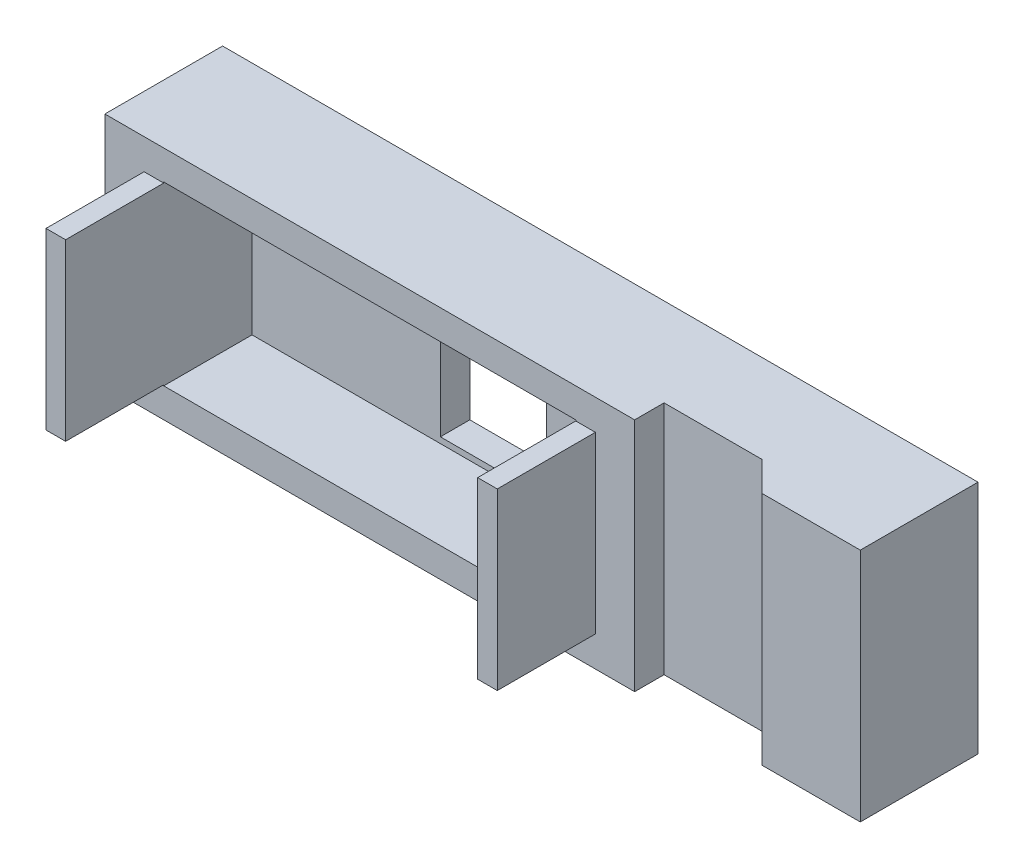
SolidWorks part; units mm, degrees
ref_plane "前视基准面" through (0, 0, 0) normal (0, 0, 1) x (1, 0, 0)
ref_plane "上视基准面" through (0, 0, 0) normal (0, 1, 0) x (1, 0, 0)
ref_plane "右视基准面" through (0, 0, 0) normal (1, 0, 0) x (0, 0, -1)
sketch "草图1" plane through (0, 0, 0) normal (0, 0, 1) x (1, 0, 0)
  line L1 (-13.5, 6) -> (13.5, 6)
  line L2 (-13.5, 6) -> (-13.5, -6)
  line L3 (-13.5, -6) -> (13.5, -6)
  line L4 (13.5, 6) -> (13.5, -6)
  line L5 (-13.5, 6) -> (13.5, -6) construction
  line L6 (-13.5, -6) -> (13.5, 6) construction
  line L7 (-10.5, 4.5) -> (10.5, 4.5)
  line L8 (-10.5, 4.5) -> (-10.5, -4.5)
  line L9 (-10.5, -4.5) -> (10.5, -4.5)
  line L10 (10.5, 4.5) -> (10.5, -4.5)
  line L11 (-10.5, 4.5) -> (10.5, -4.5) construction
  line L12 (-10.5, -4.5) -> (10.5, 4.5) construction
  point P0 (0, 0)
  point P6 (0, 0)
  dimension "D1" = 3
  dimension "D2" = 1.5
  dimension "D3" = 21
  dimension "D4" = 9
extrude "凸台-拉伸1" add sketch "草图1" along normal blind 6
sketch "草图2" plane through (0, 0, 0) normal (0, 0, -1) x (-1, 0, 0)
  line L1 (-10.5, 4.5) -> (10.5, 4.5)
  line L2 (-10.5, 4.5) -> (-10.5, -4.5)
  line L3 (-10.5, -4.5) -> (10.5, -4.5)
  line L4 (10.5, 4.5) -> (10.5, -4.5)
extrude "凸台-拉伸2" add sketch "草图2" against normal blind 1.5
sketch "草图3" plane through (0, 0, 1.5) normal (0, 0, 1) x (1, 0, 0)
  line L0 (10.5, -4.5) -> (10.5, 4.5) construction
  line L1 (-0.9, 4) -> (4.5, 4)
  line L2 (-0.9, 4) -> (-0.9, -4.2)
  line L3 (-0.9, -4.2) -> (4.5, -4.2)
  line L4 (4.5, 4) -> (4.5, -4.2)
  dimension "D1" = 5.4
  dimension "D2" = 8.2
  dimension "D3" = 4
  dimension "D4" = 6
extrude "切除-拉伸1" cut sketch "草图3" against normal through all
sketch "草图4" plane through (0, 0, 6) normal (0, 0, 1) x (1, 0, 0)
  line L0 (-10.5, 4.5) -> (-10.5, -4.5) construction
  line L1 (-10.5, 4.45) -> (-11.5, 4.45)
  line L2 (-10.5, 4.45) -> (-10.5, -4.45)
  line L3 (-10.5, -4.45) -> (-11.5, -4.45)
  line L4 (-11.5, 4.45) -> (-11.5, -4.45)
  line L5 (10.5, -4.5) -> (10.5, 4.5) construction
  line L6 (10.5, 4.45) -> (11.5, 4.45)
  line L7 (10.5, 4.45) -> (10.5, -4.45)
  line L8 (10.5, -4.45) -> (11.5, -4.45)
  line L9 (11.5, 4.45) -> (11.5, -4.45)
  dimension "D1" = 8.9
  dimension "D2" = 8.9
  dimension "D3" = 4.45
  dimension "D4" = 4.45
  dimension "D5" = 1
  dimension "D6" = 1
extrude "凸台-拉伸3" add sketch "草图4" along normal blind 5
sketch "草图6" plane through (0, 4.45, 0) normal (0, 1, 0) x (1, 0, 0)
  line L0 (-11.5, -11) -> (-12.7, -10)
  line L1 (-12.7, -10) -> (-11.5, -10)
  line L2 (-11.5, -11) -> (-11.5, -6) construction
  line L3 (-11.5, -10) -> (-11.5, -11)
  line L4 (11.5, -11) -> (12.7, -10)
  line L5 (12.7, -10) -> (11.5, -10)
  line L6 (11.5, -11) -> (11.5, -6) construction
  line L7 (11.5, -10) -> (11.5, -11)
  dimension "D1" = 1.2
  dimension "D2" = 1
  dimension "D3" = 1
  dimension "D4" = 1.2
sketch "草图8" plane through (0, 6, 0) normal (0, 1, 0) x (1, 0, 0)
  line L0 (13.5, -4.5) -> (18.5, -4.5)
  line L1 (13.5, -6) -> (13.5, 0) construction
  line L2 (18.5, -4.5) -> (20, -6)
  line L3 (20, -6) -> (25, -6)
  line L4 (25, -6) -> (25, 0)
  line L5 (25, 0) -> (20, 0)
  line L8 (13.5, -1.5) -> (13.5, -4.5)
  line L11 (13.5, 0) -> (-13.5, 0) construction
  line L12 (20, 0) -> (13.5, 0)
  line L13 (13.5, 0) -> (13.5, -1.5)
  dimension "D2" = 0
  dimension "D4" = 5
  dimension "D6" = 6
  dimension "D7" = 5
  dimension "D9" = 1.5
extrude "凸台-拉伸5" add sketch "草图8" against normal up to surface (12 mm away) up to face at (0, -6, 3)
sketch "草图9" plane through (0, 0, 0) normal (0, 0, -1) x (-1, 0, 0)
  line L0 (-25, -6) -> (-25, 6) construction
  circle A0 centre (-22, 0) radius 1.55
  dimension "D1" = 3.1
  dimension "D2" = 3
extrude "切除-拉伸2" cut sketch "草图9" against normal blind 3.5
sketch "草图10" plane through (0, 0, 1.5) normal (0, 0, 1) x (1, 0, 0)
  line L0 (10.5, 4.45) -> (10.5, -4.45) construction
  circle A0 centre (6.35, 0) radius 2
  dimension "D2" = 4
  dimension "D1" = 4.15
